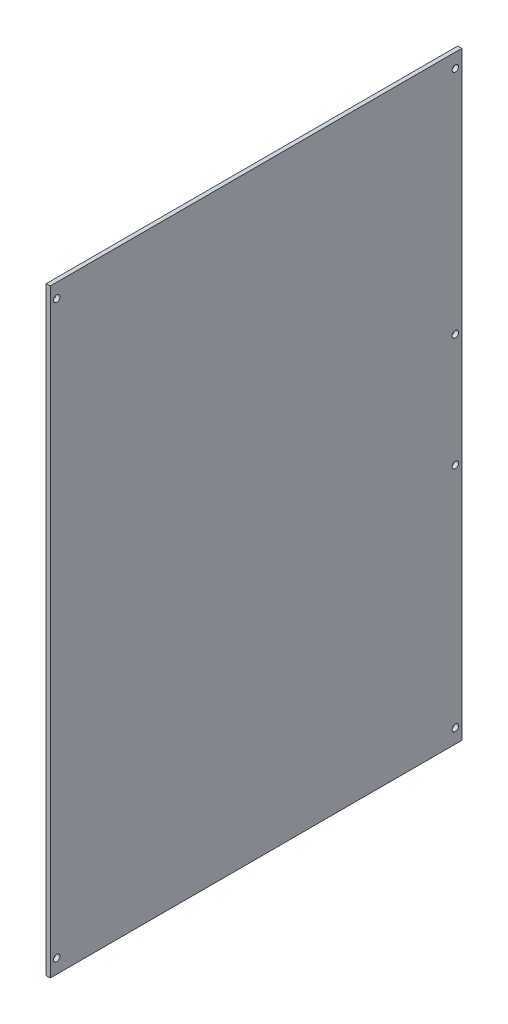
SolidWorks part; units mm, degrees
ref_plane "Front Plane" through (0, 0, 0) normal (0, 0, 1) x (1, 0, 0)
ref_plane "Top Plane" through (0, 0, 0) normal (0, 1, 0) x (1, 0, 0)
ref_plane "Right Plane" through (0, 0, 0) normal (1, 0, 0) x (0, 0, -1)
sketch "Sketch1" plane through (0, 0, 0) normal (1, 0, 0) x (0, 0, -1)
  line L1 (0, 0) -> (160, 0)
  line L2 (0, 0) -> (0, 233)
  line L3 (0, 233) -> (160, 233)
  line L4 (160, 0) -> (160, 233)
  circle A0 centre (2.5, 227.5) radius 1.25
  circle A1 centre (157.5, 227.5) radius 1.25
  circle A2 centre (157.5, 5.5) radius 1.25
  circle A3 centre (2.5, 5.5) radius 1.25
  circle A4 centre (157.5, 94) radius 1.25
  circle A5 centre (157.5, 138) radius 1.25
  dimension "D1" = 2
  dimension "D2" = 2
extrude "Boss-Extrude1" add sketch "Sketch1" along normal blind 1.5875
